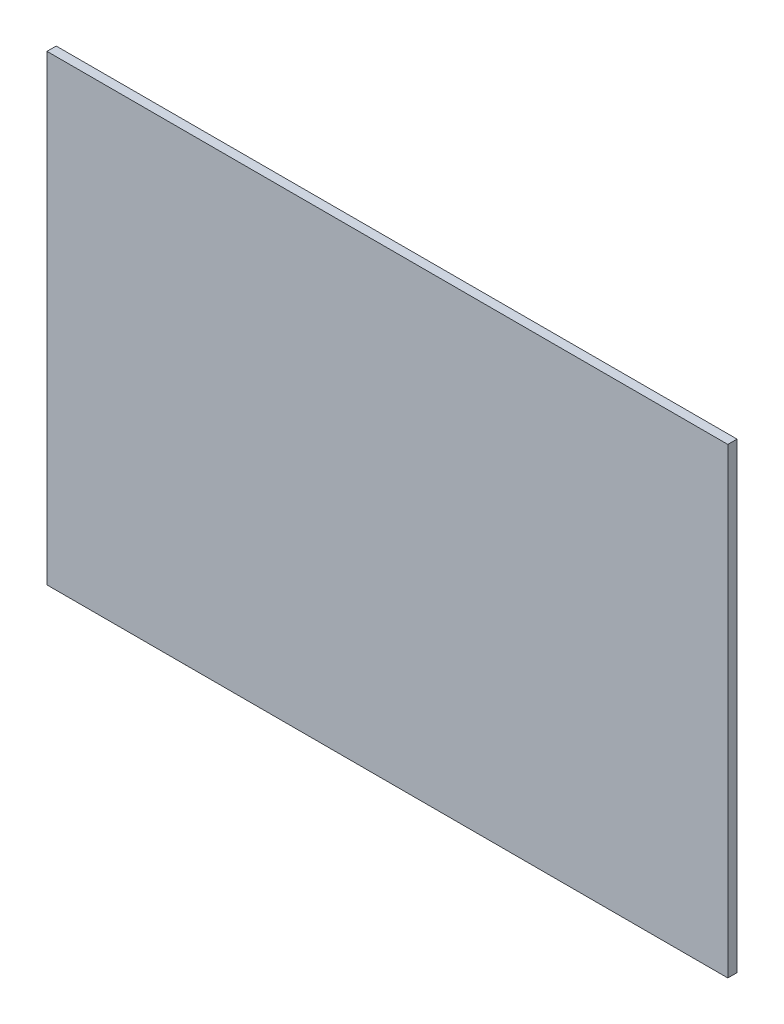
SolidWorks part; units mm, degrees
material "Plain Carbon Steel"
ref_plane "Front Plane" through (0, 0, 0) normal (0, 0, 1) x (1, 0, 0)
ref_plane "Top Plane" through (0, 0, 0) normal (0, 1, 0) x (1, 0, 0)
ref_plane "Right Plane" through (0, 0, 0) normal (1, 0, 0) x (0, 0, -1)
sketch "Sketch1" plane through (0, 0, 0) normal (0, 0, 1) x (1, 0, 0)
  line L1 (0, 0) -> (112.268, 0)
  line L2 (0, 0) -> (0, 76.2)
  line L3 (0, 76.2) -> (112.268, 76.2)
  line L4 (112.268, 0) -> (112.268, 76.2)
  dimension "D1" = 112.268
  dimension "D2" = 76.2
extrude "Boss-Extrude1" add sketch "Sketch1" along normal blind 1.5189
